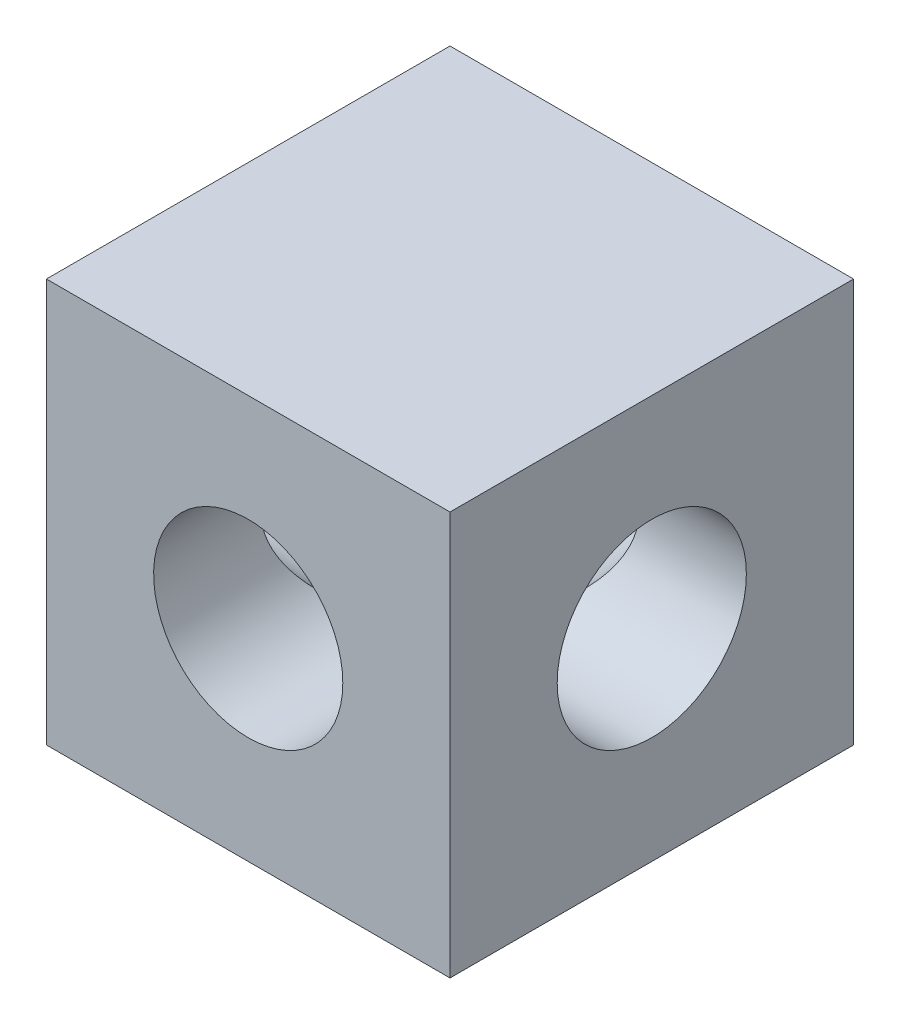
SolidWorks part; units mm, degrees
ref_plane "Front Plane" through (0, 0, 0) normal (0, 0, 1) x (1, 0, 0)
ref_plane "Top Plane" through (0, 0, 0) normal (0, 1, 0) x (1, 0, 0)
ref_plane "Right Plane" through (0, 0, 0) normal (1, 0, 0) x (0, 0, -1)
sketch "Sketch1" plane through (0, 0, 0) normal (0, 0, 1) x (1, 0, 0)
  line L1 (-10.16, -10.16) -> (10.16, -10.16)
  line L2 (-10.16, -10.16) -> (-10.16, 10.16)
  line L3 (-10.16, 10.16) -> (10.16, 10.16)
  line L4 (10.16, -10.16) -> (10.16, 10.16)
  line L5 (-10.16, -10.16) -> (10.16, 10.16) construction
  line L6 (-10.16, 10.16) -> (10.16, -10.16) construction
  circle A0 centre (0, 0) radius 4.7625
  point P0 (0, 0)
  dimension "D3" = 9.525
  dimension "D1" = 20.32
  dimension "D2" = 20.32
extrude "Boss-Extrude1" add sketch "Sketch1" along normal mid plane 20.32
sketch "Sketch2" plane through (10.16, 0, 0) normal (1, 0, 0) x (0, 0, -1)
  circle A0 centre (0, 0) radius 4.7625
  dimension "D1" = 9.525
extrude "Cut-Extrude1" cut sketch "Sketch2" against normal through all
